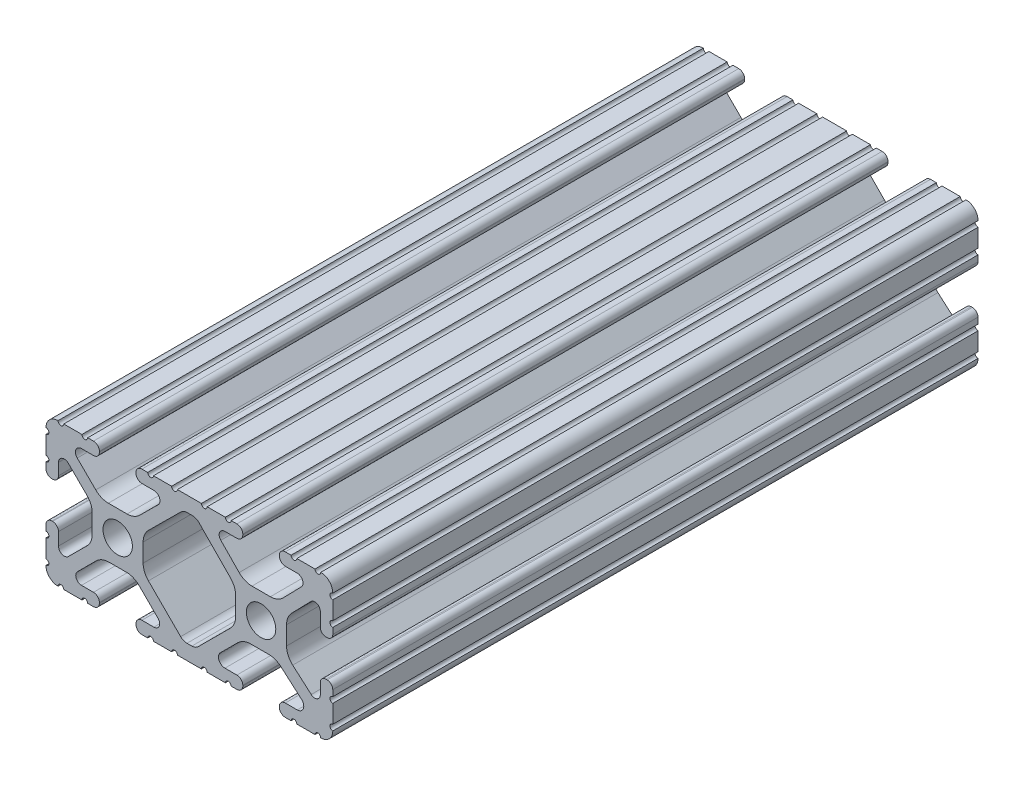
SolidWorks part; units mm, degrees
ref_plane "Front Plane" through (0, 0, 0) normal (0, 0, 1) x (1, 0, 0)
ref_plane "Top Plane" through (0, 0, 0) normal (0, 1, 0) x (1, 0, 0)
ref_plane "Right Plane" through (0, 0, 0) normal (1, 0, 0) x (0, 0, -1)
sketch "Sketch1" plane through (0, 0, 0) normal (0, 0, 1) x (1, 0, 0)
  line L0 (-7.2595, -3.8694) -> (-1.5457, -9.5728)
  line L1 (-8.1915, 1.6223) -> (-8.1915, -1.6223)
  line L2 (-1.504, 9.5765) -> (-7.252, 3.8768)
  line L3 (0.5515, 10.033) -> (-0.3952, 10.033)
  line L4 (7.2829, 3.8459) -> (1.6756, 9.5611)
  line L5 (8.1915, -1.6223) -> (8.1915, 1.6223)
  line L6 (1.5457, -9.5728) -> (7.2595, -3.8694)
  line L7 (-0.4332, -10.033) -> (0.4332, -10.033)
  line L8 (18.0171, 12.7) -> (16.9875, 12.7)
  line L9 (15.9385, 11.651) -> (15.9385, 11.5392)
  line L10 (16.9875, 10.4902) -> (19.1164, 10.4902)
  line L11 (19.8441, 8.7652) -> (16.619, 5.4551)
  line L12 (14.3449, 4.4958) -> (11.0833, 4.4958)
  line L13 (8.817, 5.4472) -> (5.5642, 8.7627)
  line L14 (6.2894, 10.4902) -> (8.4125, 10.4902)
  line L15 (9.4615, 11.5392) -> (9.4615, 11.651)
  line L16 (8.4125, 12.7) -> (7.3829, 12.7)
  line L17 (6.3669, 12.7) -> (3.1496, 12.7)
  line L18 (2.1336, 12.7) -> (-2.1336, 12.7)
  line L19 (-3.1496, 12.7) -> (-6.3669, 12.7)
  line L20 (-7.3829, 12.7) -> (-8.4125, 12.7)
  line L21 (-9.4615, 11.651) -> (-9.4615, 11.5392)
  line L22 (-8.4125, 10.4902) -> (-6.2836, 10.4902)
  line L23 (-5.5326, 8.6661) -> (-8.81, 5.4163)
  line L24 (-11.0455, 4.4958) -> (-14.3545, 4.4958)
  line L25 (-16.59, 5.4163) -> (-19.8674, 8.6661)
  line L26 (-19.1164, 10.4902) -> (-16.9875, 10.4902)
  line L27 (-15.9385, 11.5392) -> (-15.9385, 11.651)
  line L28 (-16.9875, 12.7) -> (-18.0171, 12.7)
  line L29 (-19.0331, 12.7) -> (-22.2504, 12.7)
  line L30 (-25.4, 9.5504) -> (-25.4, 6.3331)
  line L31 (-25.4, 5.3171) -> (-25.4, 4.2375)
  line L32 (-24.401, 3.2385) -> (-24.2392, 3.2385)
  line L33 (-23.1902, 4.2875) -> (-23.1902, 6.3347)
  line L34 (-21.434, 7.0665) -> (-18.148, 3.8082)
  line L35 (-17.2085, 1.5536) -> (-17.2085, -1.6952)
  line L36 (-18.1405, -3.9423) -> (-21.4316, -7.2274)
  line L37 (-23.1902, -6.498) -> (-23.1902, -4.2875)
  line L38 (-24.2392, -3.2385) -> (-24.351, -3.2385)
  line L39 (-25.4, -4.2875) -> (-25.4, -5.3171)
  line L40 (-25.4, -6.3331) -> (-25.4, -9.5504)
  line L41 (-22.2504, -12.7) -> (-19.0331, -12.7)
  line L42 (-18.0171, -12.7) -> (-16.9875, -12.7)
  line L43 (-15.9384, -11.651) -> (-15.9384, -11.5392)
  line L44 (-16.9875, -10.4902) -> (-19.1164, -10.4902)
  line L45 (-19.8341, -8.7551) -> (-16.4966, -5.4237)
  line L46 (-14.2536, -4.4958) -> (-11.1464, -4.4958)
  line L47 (-8.9034, -5.4237) -> (-5.5659, -8.7551)
  line L48 (-6.2836, -10.4902) -> (-8.4125, -10.4902)
  line L49 (-9.4616, -11.5392) -> (-9.4616, -11.651)
  line L50 (-8.4125, -12.7) -> (-7.3829, -12.7)
  line L51 (-6.3669, -12.7) -> (-3.1496, -12.7)
  line L52 (-2.1336, -12.7) -> (2.1336, -12.7)
  line L53 (3.1496, -12.7) -> (6.3669, -12.7)
  line L54 (7.3829, -12.7) -> (8.4125, -12.7)
  line L55 (9.4616, -11.651) -> (9.4616, -11.5392)
  line L56 (8.4125, -10.4902) -> (6.2894, -10.4902)
  line L57 (5.4807, -8.5353) -> (8.5979, -5.4237)
  line L58 (10.8409, -4.4958) -> (14.1026, -4.4958)
  line L59 (16.1879, -5.2766) -> (19.8682, -8.4822)
  line L60 (19.1164, -10.4902) -> (16.9875, -10.4902)
  line L61 (15.9384, -11.5392) -> (15.9384, -11.651)
  line L62 (16.9875, -12.7) -> (18.0171, -12.7)
  line L63 (19.0331, -12.7) -> (22.2504, -12.7)
  line L64 (25.4, -9.5504) -> (25.4, -6.3331)
  line L65 (25.4, -5.3171) -> (25.4, -4.2375)
  line L66 (24.401, -3.2385) -> (24.1892, -3.2385)
  line L67 (23.1902, -4.2375) -> (23.1902, -6.1559)
  line L68 (21.584, -6.8869) -> (18.2982, -4.025)
  line L69 (17.2085, -1.6308) -> (17.2085, 1.6308)
  line L70 (18.1094, 3.8465) -> (21.5263, 7.3534)
  line L71 (23.1902, 6.6769) -> (23.1902, 4.2375)
  line L72 (24.1892, 3.2385) -> (24.401, 3.2385)
  line L73 (25.4, 4.2375) -> (25.4, 5.3171)
  line L74 (25.4, 6.3332) -> (25.4, 9.5504)
  line L75 (22.2504, 12.7) -> (19.0331, 12.7)
  circle A0 centre (-12.7, 0) radius 2.6035
  circle A1 centre (12.7, 0) radius 2.6035
  arc A2 (-1.5457, -9.5728) -> (-0.4332, -10.033) centre (-0.4332, -8.4582) ccw
  arc A3 (-8.1915, -1.6223) -> (-7.2595, -3.8694) centre (-5.0165, -1.6223) ccw
  arc A4 (-7.252, 3.8768) -> (-8.1915, 1.6223) centre (-5.0165, 1.6223) ccw
  arc A5 (-0.3952, 10.033) -> (-1.504, 9.5765) centre (-0.3952, 8.4582) ccw
  arc A6 (1.6756, 9.5611) -> (0.5515, 10.033) centre (0.5515, 8.4582) ccw
  arc A7 (8.1915, 1.6223) -> (7.2829, 3.8459) centre (5.0165, 1.6223) ccw
  arc A8 (7.2595, -3.8694) -> (8.1915, -1.6223) centre (5.0165, -1.6223) ccw
  arc A9 (0.4332, -10.033) -> (1.5457, -9.5728) centre (0.4332, -8.4582) ccw
  arc A10 (18.0171, 12.7) -> (19.0331, 12.7) centre (18.5251, 12.7) ccw
  arc A11 (16.9875, 12.7) -> (15.9385, 11.651) centre (16.9875, 11.651) ccw
  arc A12 (15.9385, 11.5392) -> (16.9875, 10.4902) centre (16.9875, 11.5392) ccw
  arc A13 (19.8441, 8.7652) -> (19.1164, 10.4902) centre (19.1164, 9.4742) ccw
  arc A14 (14.3449, 4.4958) -> (16.619, 5.4551) centre (14.3449, 7.6708) ccw
  arc A15 (8.817, 5.4472) -> (11.0833, 4.4958) centre (11.0833, 7.6708) ccw
  arc A16 (6.2894, 10.4902) -> (5.5642, 8.7627) centre (6.2894, 9.4742) ccw
  arc A17 (8.4125, 10.4902) -> (9.4615, 11.5392) centre (8.4125, 11.5392) ccw
  arc A18 (9.4615, 11.651) -> (8.4125, 12.7) centre (8.4125, 11.651) ccw
  arc A19 (6.3669, 12.7) -> (7.3829, 12.7) centre (6.8749, 12.7) ccw
  arc A20 (2.1336, 12.7) -> (3.1496, 12.7) centre (2.6416, 12.7) ccw
  arc A21 (-3.1496, 12.7) -> (-2.1336, 12.7) centre (-2.6416, 12.7) ccw
  arc A22 (-7.3829, 12.7) -> (-6.3669, 12.7) centre (-6.8749, 12.7) ccw
  arc A23 (-8.4125, 12.7) -> (-9.4615, 11.651) centre (-8.4125, 11.651) ccw
  arc A24 (-9.4615, 11.5392) -> (-8.4125, 10.4902) centre (-8.4125, 11.5392) ccw
  arc A25 (-5.5326, 8.6661) -> (-6.2836, 10.4902) centre (-6.2836, 9.4235) ccw
  arc A26 (-11.0455, 4.4958) -> (-8.81, 5.4163) centre (-11.0455, 7.6708) ccw
  arc A27 (-16.59, 5.4163) -> (-14.3545, 4.4958) centre (-14.3545, 7.6708) ccw
  arc A28 (-19.1164, 10.4902) -> (-19.8674, 8.6661) centre (-19.1164, 9.4235) ccw
  arc A29 (-16.9875, 10.4902) -> (-15.9385, 11.5392) centre (-16.9875, 11.5392) ccw
  arc A30 (-15.9385, 11.651) -> (-16.9875, 12.7) centre (-16.9875, 11.651) ccw
  arc A31 (-19.0331, 12.7) -> (-18.0171, 12.7) centre (-18.5251, 12.7) ccw
  arc A32 (-23.2664, 12.6998) -> (-22.2504, 12.7) centre (-22.7584, 12.7) ccw
  arc A33 (-23.2664, 12.6998) -> (-25.3998, 10.5664) centre (-23.2918, 10.5918) ccw
  arc A34 (-25.4, 9.5504) -> (-25.3998, 10.5664) centre (-25.4, 10.0584) ccw
  arc A35 (-25.4, 5.3171) -> (-25.4, 6.3331) centre (-25.4, 5.8251) ccw
  arc A36 (-25.4, 4.2375) -> (-24.401, 3.2385) centre (-24.401, 4.2375) ccw
  arc A37 (-24.2392, 3.2385) -> (-23.1902, 4.2875) centre (-24.2392, 4.2875) ccw
  arc A38 (-21.434, 7.0665) -> (-23.1902, 6.3347) centre (-22.1596, 6.3347) ccw
  arc A39 (-17.2085, 1.5536) -> (-18.148, 3.8082) centre (-20.3835, 1.5536) ccw
  arc A40 (-18.1405, -3.9423) -> (-17.2085, -1.6952) centre (-20.3835, -1.6952) ccw
  arc A41 (-23.1902, -6.498) -> (-21.4316, -7.2274) centre (-22.1596, -6.498) ccw
  arc A42 (-23.1902, -4.2875) -> (-24.2392, -3.2385) centre (-24.2392, -4.2875) ccw
  arc A43 (-24.351, -3.2385) -> (-25.4, -4.2875) centre (-24.351, -4.2875) ccw
  arc A44 (-25.4, -6.3331) -> (-25.4, -5.3171) centre (-25.4, -5.8251) ccw
  arc A45 (-25.3998, -10.5664) -> (-25.4, -9.5504) centre (-25.4, -10.0584) ccw
  arc A46 (-25.3998, -10.5664) -> (-23.2664, -12.6998) centre (-23.2918, -10.5918) ccw
  arc A47 (-22.2504, -12.7) -> (-23.2664, -12.6998) centre (-22.7584, -12.7) ccw
  arc A48 (-18.0171, -12.7) -> (-19.0331, -12.7) centre (-18.5251, -12.7) ccw
  arc A49 (-16.9875, -12.7) -> (-15.9384, -11.651) centre (-16.9875, -11.651) ccw
  arc A50 (-15.9384, -11.5392) -> (-16.9875, -10.4902) centre (-16.9875, -11.5392) ccw
  arc A51 (-19.8341, -8.7551) -> (-19.1164, -10.4902) centre (-19.1164, -9.4742) ccw
  arc A52 (-14.2536, -4.4958) -> (-16.4966, -5.4237) centre (-14.2536, -7.6708) ccw
  arc A53 (-8.9034, -5.4237) -> (-11.1464, -4.4958) centre (-11.1464, -7.6708) ccw
  arc A54 (-6.2836, -10.4902) -> (-5.5659, -8.7551) centre (-6.2836, -9.4742) ccw
  arc A55 (-8.4125, -10.4902) -> (-9.4616, -11.5392) centre (-8.4125, -11.5392) ccw
  arc A56 (-9.4616, -11.651) -> (-8.4125, -12.7) centre (-8.4125, -11.651) ccw
  arc A57 (-6.3669, -12.7) -> (-7.3829, -12.7) centre (-6.8749, -12.7) ccw
  arc A58 (-2.1336, -12.7) -> (-3.1496, -12.7) centre (-2.6416, -12.7) ccw
  arc A59 (3.1496, -12.7) -> (2.1336, -12.7) centre (2.6416, -12.7) ccw
  arc A60 (7.3829, -12.7) -> (6.3669, -12.7) centre (6.8749, -12.7) ccw
  arc A61 (8.4125, -12.7) -> (9.4616, -11.651) centre (8.4125, -11.651) ccw
  arc A62 (9.4616, -11.5392) -> (8.4125, -10.4902) centre (8.4125, -11.5392) ccw
  arc A63 (5.4807, -8.5353) -> (6.2894, -10.4902) centre (6.2894, -9.3455) ccw
  arc A64 (10.8409, -4.4958) -> (8.5979, -5.4237) centre (10.8409, -7.6708) ccw
  arc A65 (16.1879, -5.2766) -> (14.1026, -4.4958) centre (14.1026, -7.6708) ccw
  arc A66 (19.1164, -10.4902) -> (19.8682, -8.4822) centre (19.1164, -9.3455) ccw
  arc A67 (16.9875, -10.4902) -> (15.9384, -11.5392) centre (16.9875, -11.5392) ccw
  arc A68 (15.9384, -11.651) -> (16.9875, -12.7) centre (16.9875, -11.651) ccw
  arc A69 (19.0331, -12.7) -> (18.0171, -12.7) centre (18.5251, -12.7) ccw
  arc A70 (23.2664, -12.6998) -> (22.2504, -12.7) centre (22.7584, -12.7) ccw
  arc A71 (23.2664, -12.6998) -> (25.3998, -10.5664) centre (23.2918, -10.5918) ccw
  arc A72 (25.4, -9.5504) -> (25.3998, -10.5664) centre (25.4, -10.0584) ccw
  arc A73 (25.4, -5.3171) -> (25.4, -6.3331) centre (25.4, -5.8251) ccw
  arc A74 (25.4, -4.2375) -> (24.401, -3.2385) centre (24.401, -4.2375) ccw
  arc A75 (24.1892, -3.2385) -> (23.1902, -4.2375) centre (24.1892, -4.2375) ccw
  arc A76 (21.584, -6.8869) -> (23.1902, -6.1559) centre (22.2207, -6.1559) ccw
  arc A77 (17.2085, -1.6308) -> (18.2982, -4.025) centre (20.3835, -1.6308) ccw
  arc A78 (18.1094, 3.8465) -> (17.2085, 1.6308) centre (20.3835, 1.6308) ccw
  arc A79 (23.1902, 6.6769) -> (21.5263, 7.3534) centre (22.2207, 6.6769) ccw
  arc A80 (23.1902, 4.2375) -> (24.1892, 3.2385) centre (24.1892, 4.2375) ccw
  arc A81 (24.401, 3.2385) -> (25.4, 4.2375) centre (24.401, 4.2375) ccw
  arc A82 (25.4, 6.3332) -> (25.4, 5.3171) centre (25.4, 5.8251) ccw
  arc A83 (25.3998, 10.5664) -> (25.4, 9.5504) centre (25.4, 10.0584) ccw
  arc A84 (25.3998, 10.5664) -> (23.2664, 12.6998) centre (23.2918, 10.5918) ccw
  arc A85 (22.2504, 12.7) -> (23.2664, 12.6998) centre (22.7584, 12.7) ccw
  point P248 (0, 10.033)
extrude "Boss-Extrude1" add sketch "Sketch1" along normal mid plane 114.3
